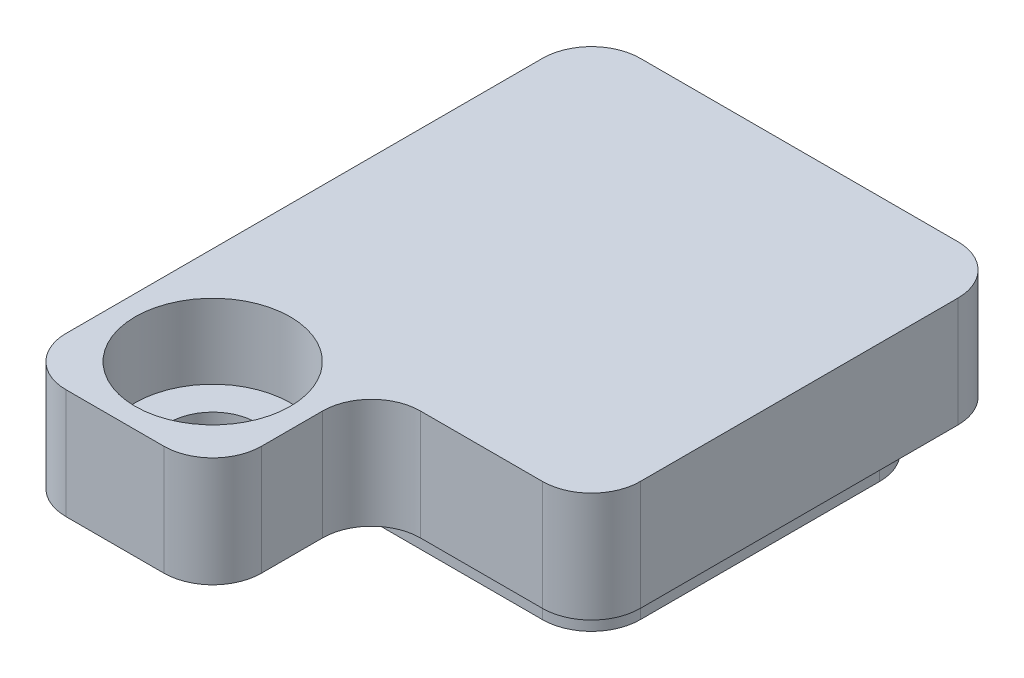
SolidWorks part; units mm, degrees
ref_plane "Front Plane" through (0, 0, 0) normal (0, 0, 1) x (1, 0, 0)
ref_plane "Top Plane" through (0, 0, 0) normal (0, 1, 0) x (1, 0, 0)
ref_plane "Right Plane" through (0, 0, 0) normal (1, 0, 0) x (0, 0, -1)
sketch "Sketch1" plane through (0, 0, 0) normal (0, 1, 0) x (1, 0, 0)
  line L1 (-4.25, -4.25) -> (4.25, -4.25)
  line L2 (-4.25, -4.25) -> (-4.25, 4.25)
  line L3 (-4.25, 4.25) -> (4.25, 4.25)
  line L4 (4.25, -4.25) -> (4.25, 4.25)
  line L5 (-4.25, -4.25) -> (4.25, 4.25) construction
  line L6 (-4.25, 4.25) -> (4.25, -4.25) construction
  point P0 (0, 0)
  dimension "D1" = 8.5
  dimension "D2" = 8.5
extrude "Extrude1" add sketch "Sketch1" along normal blind 2.25
sketch "Sketch7" plane through (0, 0, 0) normal (0, -1, 0) x (1, 0, 0)
  line L1 (-3.45, -3.45) -> (3.45, -3.45)
  line L2 (-3.45, -3.45) -> (-3.45, 3.45)
  line L3 (-3.45, 3.45) -> (3.45, 3.45)
  line L4 (3.45, -3.45) -> (3.45, 3.45)
  line L5 (-3.45, -3.45) -> (3.45, 3.45) construction
  line L6 (-3.45, 3.45) -> (3.45, -3.45) construction
  point P0 (0, 0)
  dimension "D1" = 6.9
  dimension "D2" = 6.9
extrude "Extrude5" add sketch "Sketch7" along normal blind 1
sketch "Sketch3" plane through (0, 0, 4.25) normal (0, 0, 1) x (1, 0, 0)
  line L0 (-4.25, 0) -> (4.25, 0) construction
  line L1 (-4.25, 2.25) -> (-0.25, 2.25)
  line L2 (-4.25, 2.25) -> (-4.25, 0)
  line L3 (-4.25, 0) -> (-0.25, 0)
  line L4 (-0.25, 2.25) -> (-0.25, 0)
  dimension "D1" = 4
extrude "Extrude3" add sketch "Sketch3" along normal blind 3.25
hole_wizard "CBORE for #0 Socket Head Cap Screw1" positions "3DSketch2" profile "Sketch6" counterbore size "#0" standard "Ansi Inch" end condition through all
sketch3d "3DSketch2"
  line L0 (-0.25, 2.25, 7.5) -> (-4.25, 2.25, 7.5) construction
  line L1 (-0.25, 2.25, 7.5) -> (-0.25, 2.25, 4.25) construction
  point P0 (-2.25, 2.25, 5.5)
  dimension "D1" = 2
  dimension "D2" = 2
sketch "Sketch6" plane through (-2.25, 2.25, 5.5) normal (1, 0, 0) x (0, 0, 1)
  line L0 (0, 0) -> (0, 3.25)
  line L1 (0, 3.25) -> (0.889, 3.25)
  line L3 (0.889, 3.25) -> (0.889, 1.524)
  line L4 (0.889, 1.524) -> (1.5875, 1.524)
  line L5 (1.5875, 1.524) -> (1.5875, 0)
  line L7 (1.5875, 0) -> (0, 0)
  line L11 (0, -6.35) -> (0, 107.95) construction
  dimension "Thru Hole Dia." = 1.778
  dimension "Thru Hole Depth" = 3.25
  dimension "C'Bore Dia." = 3.175
  dimension "C'Bore Depth" = 1.524
fillet "Fillet2" radius 1 10 edges at (-3.45, -0.5, -3.45) (-4.25, 1.125, -4.25) (-3.45, -0.5, 3.45) (3.45, -0.5, -3.45) (3.45, -0.5, 3.45) (4.25, 1.125, -4.25) (4.25, 1.125, 4.25) (-4.25, 1.125, 7.5) (-0.25, 1.125, 7.5)
